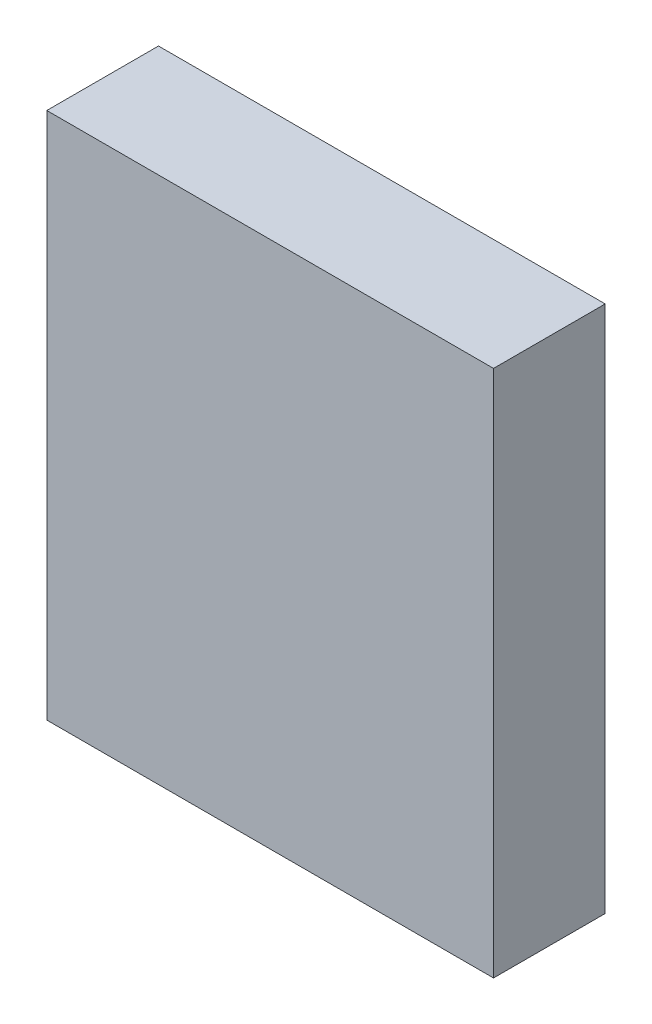
SolidWorks part; units mm, degrees
ref_plane "Piano frontale" through (0, 0, 0) normal (0, 0, 1) x (1, 0, 0)
ref_plane "Piano superiore" through (0, 0, 0) normal (0, 1, 0) x (1, 0, 0)
ref_plane "Piano destro" through (0, 0, 0) normal (1, 0, 0) x (0, 0, -1)
sketch "Schizzo1" plane through (0, 0, 0) normal (0, 0, 1) x (1, 0, 0)
  line L1 (0, 0) -> (44, 0)
  line L2 (0, 0) -> (0, 52)
  line L3 (0, 52) -> (44, 52)
  line L4 (44, 0) -> (44, 52)
  dimension "D1" = 52
  dimension "D2" = 44
extrude "Estrusione-Estrusione1" add sketch "Schizzo1" along normal blind 11
